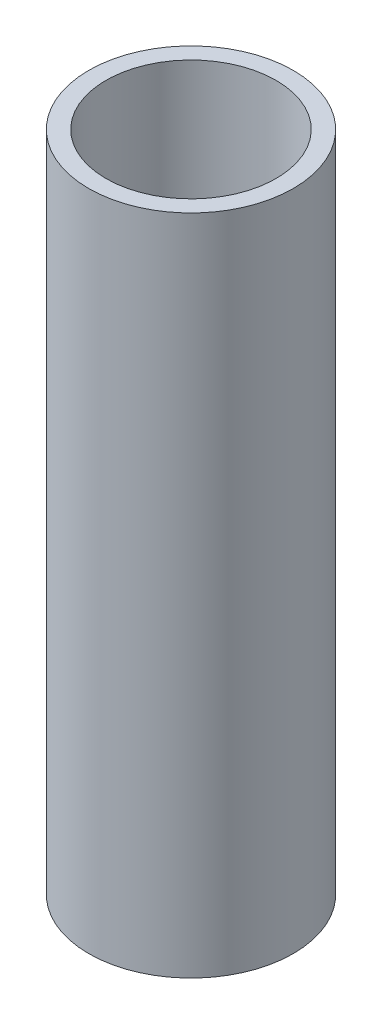
SolidWorks part; units mm, degrees
material "6061 Alloy"
ref_plane "Front Plane" through (0, 0, 0) normal (0, 0, 1) x (1, 0, 0)
ref_plane "Top Plane" through (0, 0, 0) normal (0, 1, 0) x (1, 0, 0)
ref_plane "Right Plane" through (0, 0, 0) normal (1, 0, 0) x (0, 0, -1)
sketch "Sketch1" plane through (0, 0, 0) normal (0, 1, 0) x (1, 0, 0)
  circle A0 centre (0, 0) radius 21.082
  circle A1 centre (0, 0) radius 17.526
  dimension "D1" = 42.164
  dimension "D2" = 35.052
extrude "Boss-Extrude1" add sketch "Sketch1" along normal blind 136.525
